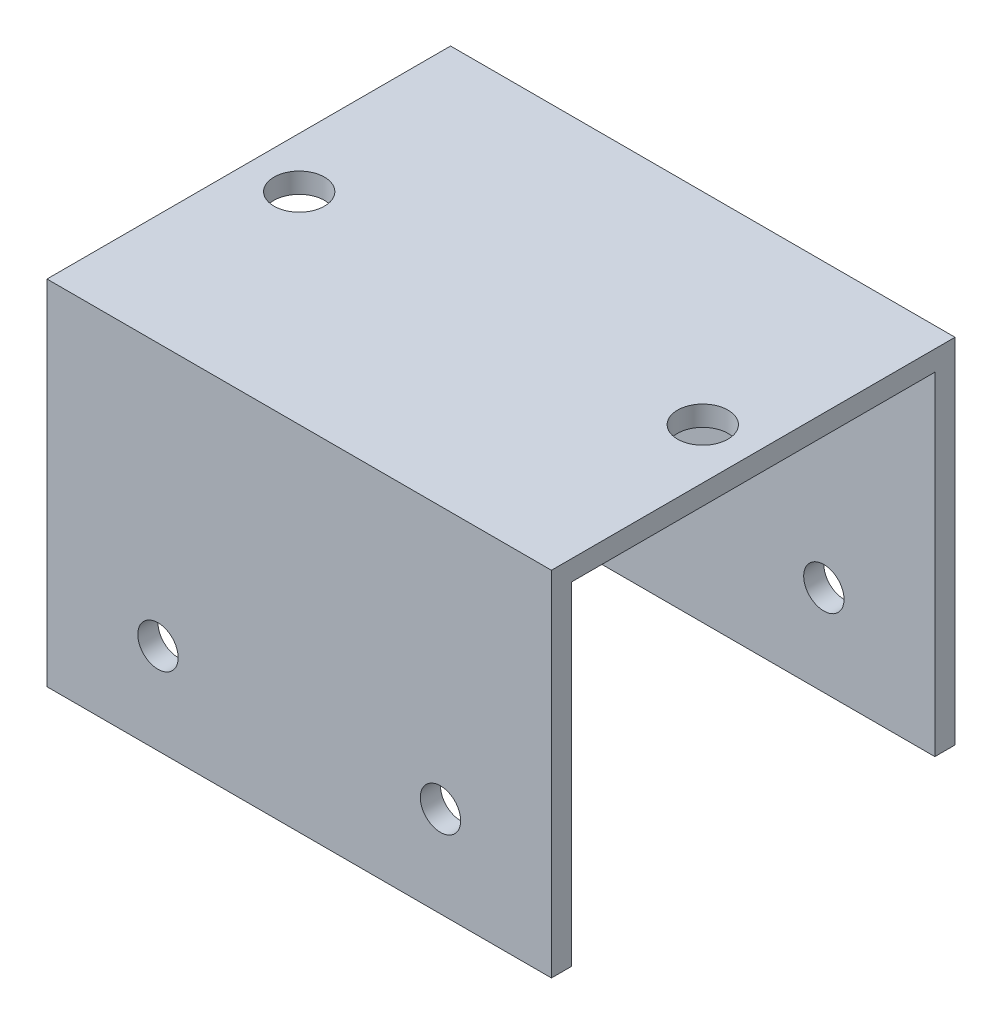
SolidWorks part; units mm, degrees
ref_plane "前视基准面" through (0, 0, 0) normal (0, 0, 1) x (1, 0, 0)
ref_plane "上视基准面" through (0, 0, 0) normal (0, 1, 0) x (1, 0, 0)
ref_plane "右视基准面" through (0, 0, 0) normal (1, 0, 0) x (0, 0, -1)
sketch "草图1" plane through (0, 0, 0) normal (1, 0, 0) x (0, 0, -1)
  line L0 (18, 33) -> (18, 0)
  line L1 (-20, 35) -> (20, 35)
  line L2 (-20, 35) -> (-20, 0)
  line L3 (-20, 0) -> (20, 0) construction
  line L4 (20, 35) -> (20, 0)
  line L5 (-20, 35) -> (20, 0) construction
  line L6 (-20, 0) -> (20, 35) construction
  line L7 (-18, 33) -> (18, 33)
  line L8 (-18, 33) -> (-18, 0)
  line L9 (-20, 0) -> (-18, 0)
  line L10 (18, 0) -> (20, 0)
  point P0 (0, 17.5)
  dimension "D1" = 40
  dimension "D2" = 35
  dimension "D3" = 2
extrude "凸台-拉伸1" add sketch "草图1" along normal mid plane 50
sketch "草图2" plane through (0, 0, 20) normal (0, 0, 1) x (1, 0, 0)
  line L0 (-14, 9) -> (14, 9) construction
  line L1 (25, 0) -> (-25, 0) construction
  circle A0 centre (-14, 9) radius 2
  circle A1 centre (14, 9) radius 2
  point P2 (0, 9)
  dimension "D1" = 28
  dimension "D2" = 9
extrude "切除-拉伸1" cut sketch "草图2" against normal through all
sketch "草图3" plane through (0, 35, 0) normal (0, 1, 0) x (1, 0, 0)
  line L9 (-20, 20) -> (-20, -20)
  line L10 (-20, 20) -> (-20, -20) construction
  line L11 (-30.4629, 0) -> (12.8324, 0) construction
  line L12 (20, 20) -> (20, -20)
  line L13 (20, 20) -> (20, -20) construction
  circle A0 centre (-20, 0) radius 2.5
  circle A1 centre (20, 0) radius 2.5
  point P6 (0, 0)
  point P7 (-47.431, -0.7128)
  dimension "D3" = 5
  dimension "D4" = 5
  dimension "D1" = 5
  dimension "D2" = 5
extrude "切除-拉伸2" cut sketch "草图3" against normal blind 10
